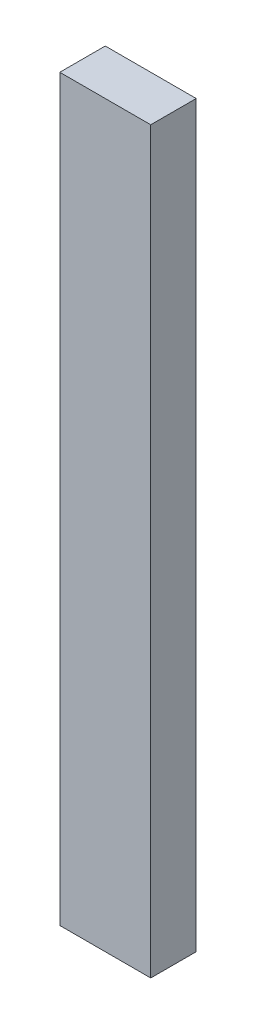
SolidWorks part; units mm, degrees
ref_plane "Front Plane" through (0, 0, 0) normal (0, 0, 1) x (1, 0, 0)
ref_plane "Top Plane" through (0, 0, 0) normal (0, 1, 0) x (1, 0, 0)
ref_plane "Right Plane" through (0, 0, 0) normal (1, 0, 0) x (0, 0, -1)
sketch "Sketch1" plane through (0, 0, 0) normal (0, 0, 1) x (1, 0, 0)
  line L1 (0, 0) -> (2.032, 0)
  line L2 (0, 0) -> (0, -16.51)
  line L3 (0, -16.51) -> (2.032, -16.51)
  line L4 (2.032, 0) -> (2.032, -16.51)
  dimension "D1" = 16.51
  dimension "D2" = 2.032
extrude "Boss-Extrude1" add sketch "Sketch1" along normal blind 1.016
